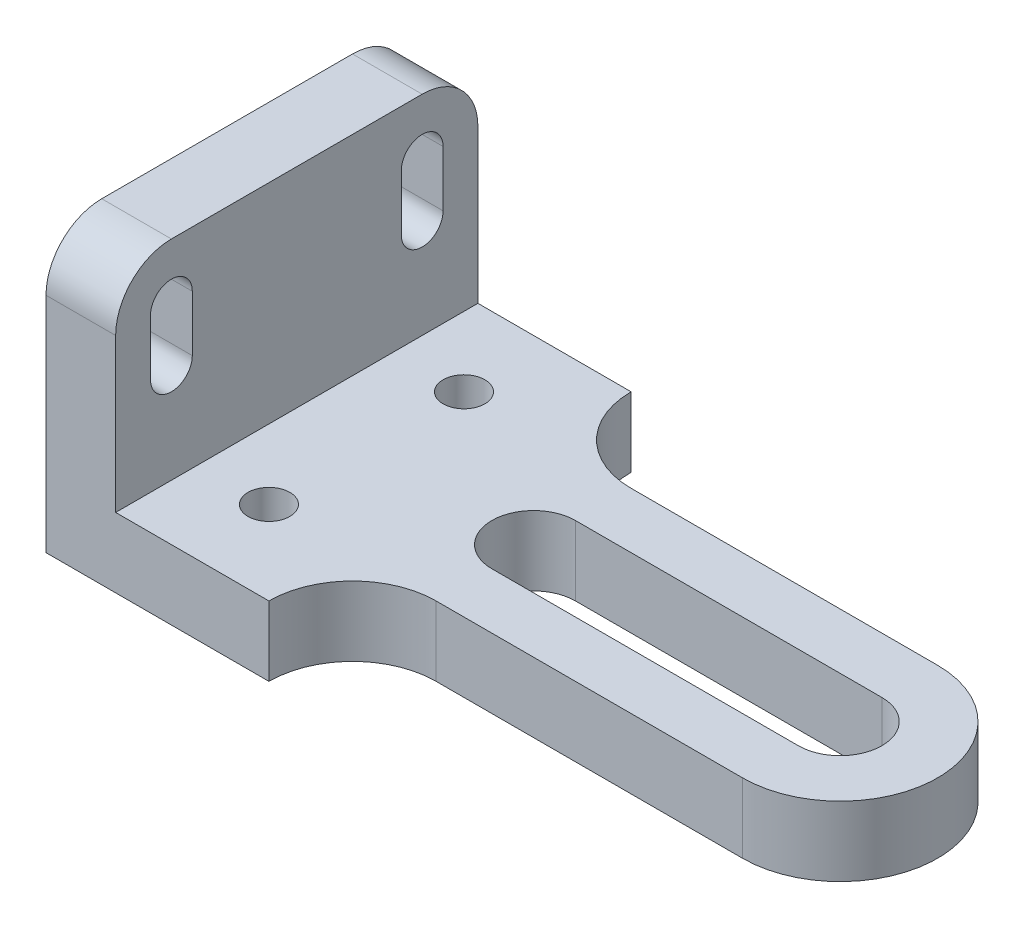
SolidWorks part; units mm, degrees
ref_plane "Front Plane" through (0, 0, 0) normal (0, 0, 1) x (1, 0, 0)
ref_plane "Top Plane" through (0, 0, 0) normal (0, 1, 0) x (1, 0, 0)
ref_plane "Right Plane" through (0, 0, 0) normal (1, 0, 0) x (0, 0, -1)
sketch "Sketch1" plane through (0, 0, 0) normal (1, 0, 0) x (0, 0, -1)
  line L0 (-26, 0) -> (26, 0)
  line L1 (26, 0) -> (26, 32)
  line L2 (18, 40) -> (-18, 40)
  line L3 (-26, 32) -> (-26, 0)
  line L4 (-18, 32) -> (-18, 24) construction
  line L5 (-15, 32) -> (-15, 24)
  line L6 (-21, 32) -> (-21, 24)
  line L7 (0, 55.751) -> (0, -21.0414) construction
  line L8 (18, 32) -> (18, 24) construction
  line L9 (15, 32) -> (15, 24)
  line L10 (21, 32) -> (21, 24)
  arc A0 (26, 32) -> (18, 40) centre (18, 32) ccw
  arc A1 (-18, 40) -> (-26, 32) centre (-18, 32) ccw
  arc A2 (-15, 32) -> (-21, 32) centre (-18, 32) ccw
  arc A3 (-21, 24) -> (-15, 24) centre (-18, 24) ccw
  arc A4 (15, 32) -> (21, 32) centre (18, 32) cw
  arc A5 (21, 24) -> (15, 24) centre (18, 24) cw
  point P3 (0, 0)
  point P11 (-26, 40)
  point P14 (-18, 28)
  point P22 (18, 28)
  dimension "D3" = 8
  dimension "D1" = 40
  dimension "D2" = 52
  dimension "D4" = 6
  dimension "D5" = 18
  dimension "D6" = 24
  dimension "D7" = 8
extrude "Boss-Extrude1" add sketch "Sketch1" along normal blind 10
sketch "Sketch2" plane through (0, 0, 0) normal (0, 1, 0) x (1, 0, 0)
  line L0 (0, 26) -> (32, 26)
  line L1 (44, 14) -> (88, 14)
  line L2 (-5.0098, 0) -> (119.6783, 0) construction
  line L3 (0, 26) -> (0, -26)
  line L4 (44, -14) -> (88, -14)
  line L5 (0, -26) -> (32, -26)
  line L6 (44, 0) -> (88, 0) construction
  line L7 (44, 6) -> (88, 6)
  line L8 (44, -6) -> (88, -6)
  arc A0 (32, 26) -> (44, 14) centre (44, 26) ccw
  arc A1 (88, 14) -> (88, -14) centre (88, 0) cw
  arc A2 (32, -26) -> (44, -14) centre (44, -26) cw
  arc A3 (44, 6) -> (44, -6) centre (44, 0) ccw
  arc A4 (88, -6) -> (88, 6) centre (88, 0) ccw
  circle A5 centre (20, 14) radius 3
  circle A6 centre (20, -14) radius 3
  point P13 (0, 0)
  point P17 (66, 0)
  dimension "D6" = 6
  dimension "D1" = 32
  dimension "D2" = 44
  dimension "D3" = 88
  dimension "D4" = 12
  dimension "D5" = 28
  dimension "D7" = 20
extrude "Boss-Extrude2" add sketch "Sketch2" along normal blind 10
